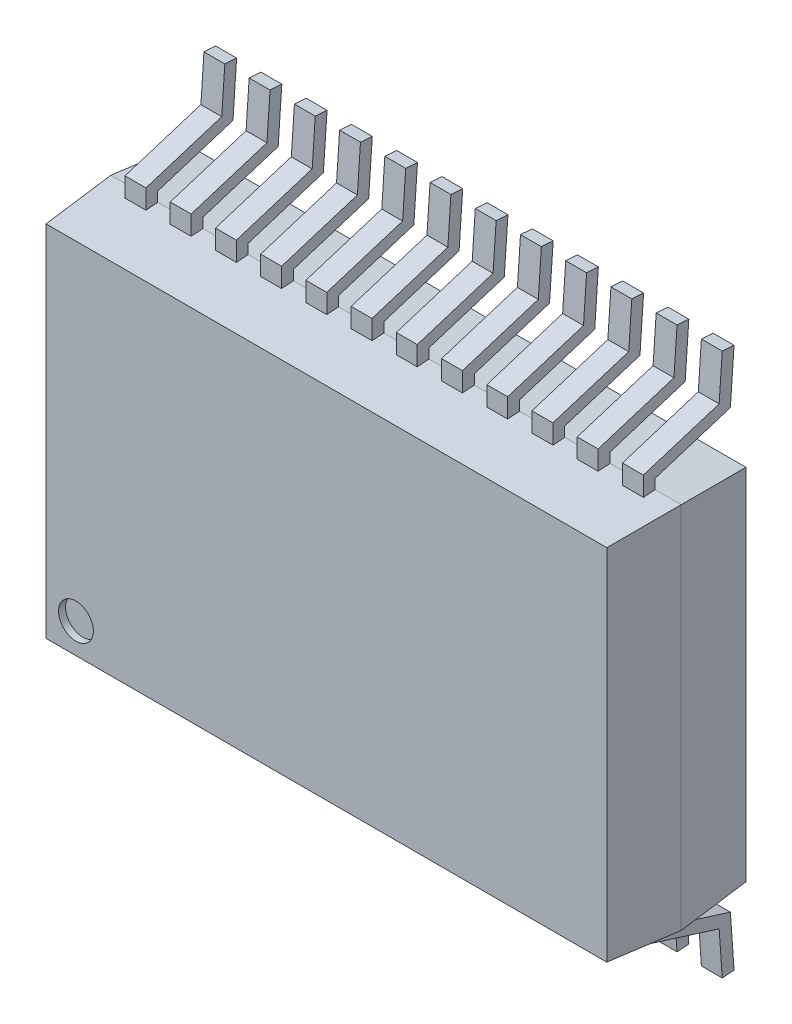
SolidWorks part; units mm, degrees
ref_plane "Front Plane" through (0, 0, 0) normal (0, 0, 1) x (1, 0, 0)
ref_plane "Top Plane" through (0, 0, 0) normal (0, 1, 0) x (1, 0, 0)
ref_plane "Right Plane" through (0, 0, 0) normal (1, 0, 0) x (0, 0, -1)
sketch "Sketch1" plane through (0, 0, 0) normal (0, 0, 1) x (1, 0, 0)
  line L1 (0, 0) -> (8.2, 0)
  line L2 (0, 0) -> (0, 5.3)
  line L3 (0, 5.3) -> (8.2, 5.3)
  line L4 (8.2, 0) -> (8.2, 5.3)
  dimension "D1" = 5.3
  dimension "D2" = 8.2
extrude "Boss-Extrude1" add sketch "Sketch1" along normal blind 1 draft 4
mirror "Mirror1" about plane through (0, 0, 0) normal (0, 0, 1) of "Boss-Extrude1"
ref_plane "Plane1" through (0.525, 0, 0) normal (1, 0, 0) x (0, 0, -1)
sketch "Sketch2" plane through (0.525, 0, 0) normal (1, 0, 0) x (0, 0, -1)
  line L0 (0, 0) -> (0, -0.161)
  line L1 (0, -0.161) -> (1.0815, -0.5)
  line L2 (1.0815, -0.5) -> (1.134, -1.25)
  line L3 (1.0815, -0.5) -> (1.0815, -1.0918) construction
  dimension "D1" = 4
  dimension "D2" = 0.75
  dimension "D3" = 1.25
extrude "Extrude-Thin1" add sketch "Sketch2" along normal mid plane 0.3 separate body thin
pattern_linear "LPattern1" count 12 spacing 0.65 along (1, 0, 0) of "Extrude-Thin1"
ref_plane "Plane2" through (0, 2.64, 0) normal (0, 1, 0) x (1, 0, 0)
mirror "Mirror2" about plane through (0, 2.64, 0) normal (0, 1, 0) of "Extrude-Thin1", "LPattern1"
sketch "Sketch3" plane through (0, 0, 1) normal (0, 0, 1) x (1, 0, 0)
  line L0 (0, 0) -> (8.2, 0) construction
  line L1 (0, 5.3) -> (0, 0) construction
  circle A0 centre (0.5, 0.5) radius 0.25
  dimension "D1" = 0.5
  dimension "D2" = 0.5
  dimension "D3" = 0.5
extrude "Cut-Extrude1" cut sketch "Sketch3" against normal blind 0.1
